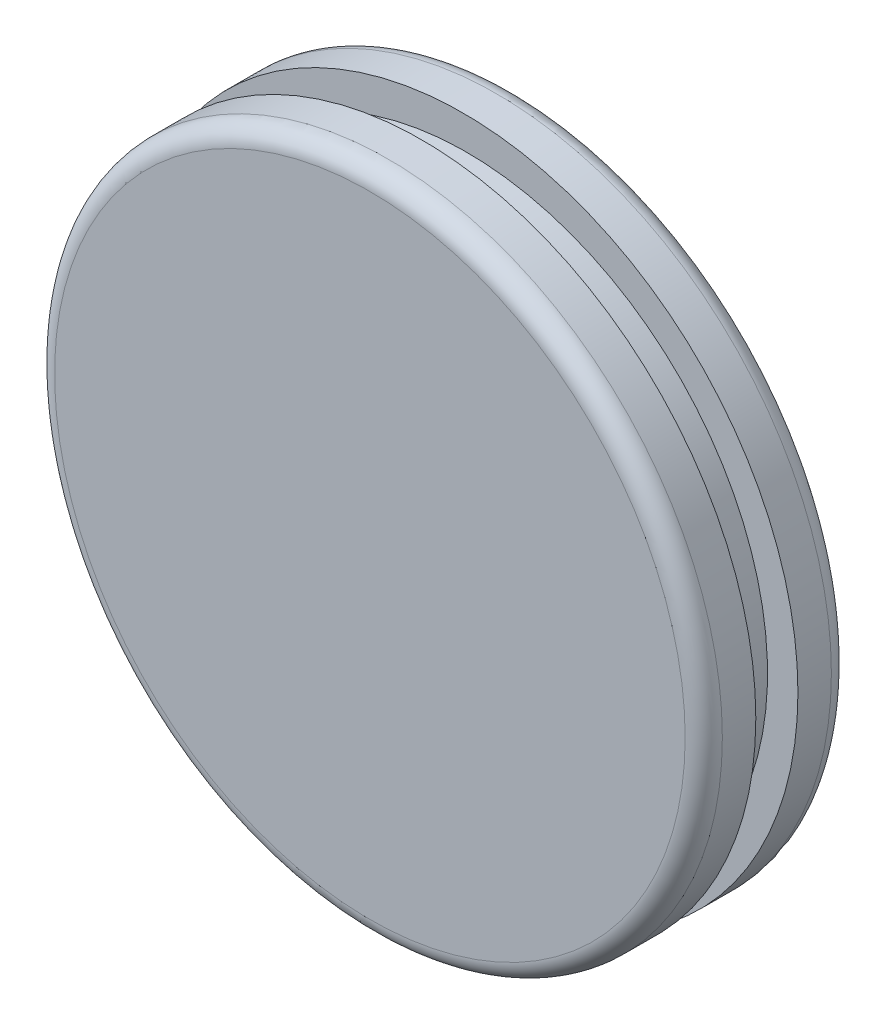
SolidWorks part; units mm, degrees
ref_plane "Front Plane" through (0, 0, 0) normal (0, 0, 1) x (1, 0, 0)
ref_plane "Top Plane" through (0, 0, 0) normal (0, 1, 0) x (1, 0, 0)
ref_plane "Right Plane" through (0, 0, 0) normal (1, 0, 0) x (0, 0, -1)
sketch "Sketch1" plane through (0, 0, 0) normal (0, 0, 1) x (1, 0, 0)
  circle A0 centre (0, 0) radius 22.812
  point P3 (0, 0)
extrude "Boss-Extrude1" add sketch "Sketch1" along normal blind 3.556
sketch "Sketch2" plane through (0, 0, 0) normal (0, 0, -1) x (-1, 0, 0)
  circle A0 centre (0, 0) radius 20.5653
extrude "Boss-Extrude2" add sketch "Sketch2" along normal blind 3.048
sketch "Sketch3" plane through (-3.1187, -2.89, -3.048) normal (0, 0, -1) x (-1, 0, 0)
  circle A0 centre (-2.9007, 2.7915) radius 22.86
extrude "Boss-Extrude3" add sketch "Sketch3" along normal blind 3.556
fillet "Fillet2" radius 1.27 1 edges at (22.812, 0, 3.556)
fillet "Fillet3" radius 1.27 1 edges at (-23.078, -0.0985, -6.604)
